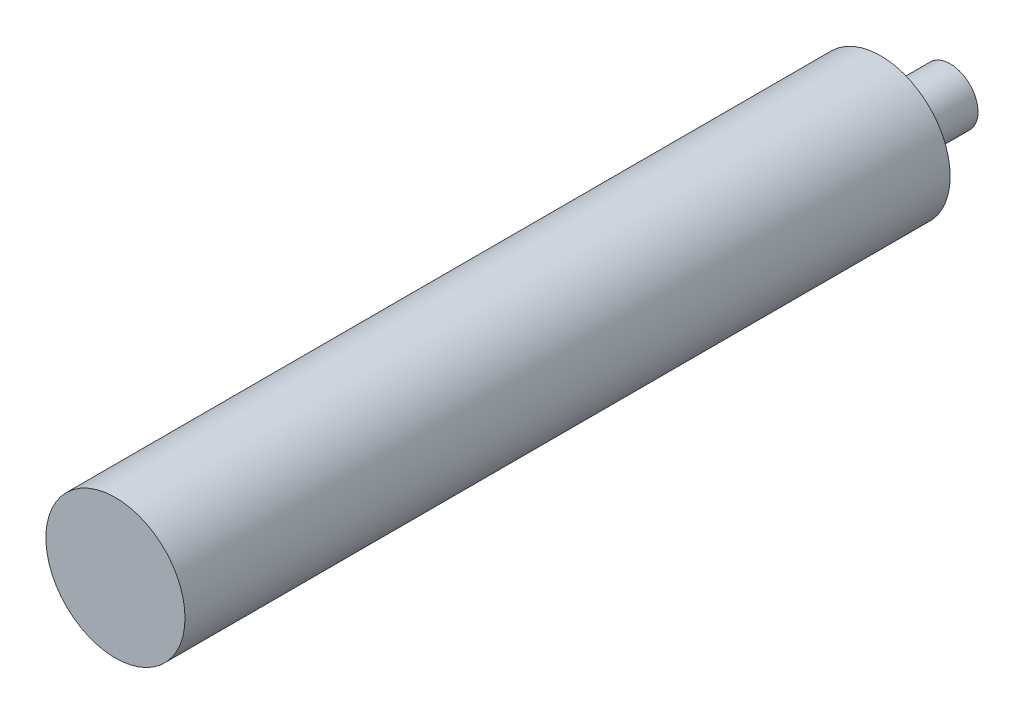
SolidWorks part; units mm, degrees
ref_plane "Front" through (0, 0, 0) normal (0, 0, 1) x (1, 0, 0)
ref_plane "Top" through (0, 0, 0) normal (0, 1, 0) x (1, 0, 0)
ref_plane "Right" through (0, 0, 0) normal (1, 0, 0) x (0, 0, -1)
sketch "Sketch1" plane through (0, 0, 0) normal (0, 0, 1) x (1, 0, 0)
  circle A0 centre (0, 0) radius 2
  dimension "D1" = 4
extrude "Boss-Extrude1" add sketch "Sketch1" along normal blind 5
sketch "Sketch2" plane through (0, 0, 5) normal (0, 0, 1) x (1, 0, 0)
  circle A0 centre (0, 0) radius 5
  dimension "D1" = 10
extrude "Boss-Extrude2" add sketch "Sketch2" along normal blind 55
